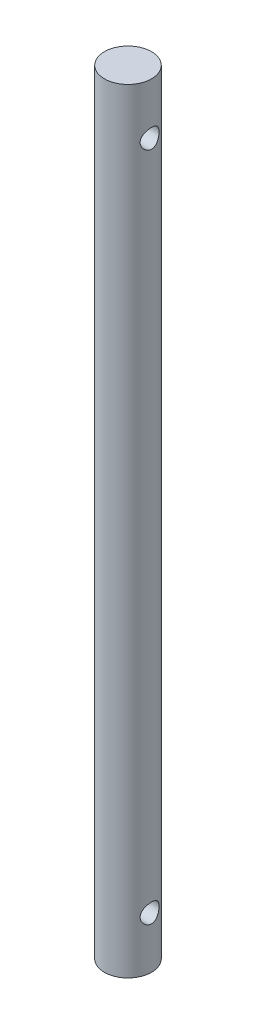
SolidWorks part; units mm, degrees
ref_plane "Front Plane" through (0, 0, 0) normal (0, 0, 1) x (1, 0, 0)
ref_plane "Top Plane" through (0, 0, 0) normal (0, 1, 0) x (1, 0, 0)
ref_plane "Right Plane" through (0, 0, 0) normal (1, 0, 0) x (0, 0, -1)
sketch "Sketch1" plane through (0, 0, 0) normal (0, 1, 0) x (1, 0, 0)
  circle A0 centre (0, 0) radius 3.9624
  dimension "D1" = 7.9248
extrude "Boss-Extrude1" add sketch "Sketch1" along normal mid plane 130.175
sketch "Sketch2" plane through (0, 0, 0) normal (0, 0, 1) x (1, 0, 0)
  line L0 (3.9624, 65.0875) -> (-3.9624, 65.0875) construction
  line L1 (14.9867, 56.4261) -> (-17.0338, 56.4261)
  line L2 (14.9867, 56.4261) -> (14.9867, 58.0136)
  line L3 (14.9867, 58.0136) -> (-17.0338, 58.0136)
  line L4 (-17.0338, 56.4261) -> (-17.0338, 58.0136)
  dimension "D1" = 1.5875
  dimension "D2" = 8.6614
revolve "Cut-Revolve1" cut sketch "Sketch2" angle 360 about L1
mirror "Mirror1" about plane through (0, 0, 0) normal (0, 1, 0) of "Cut-Revolve1"
